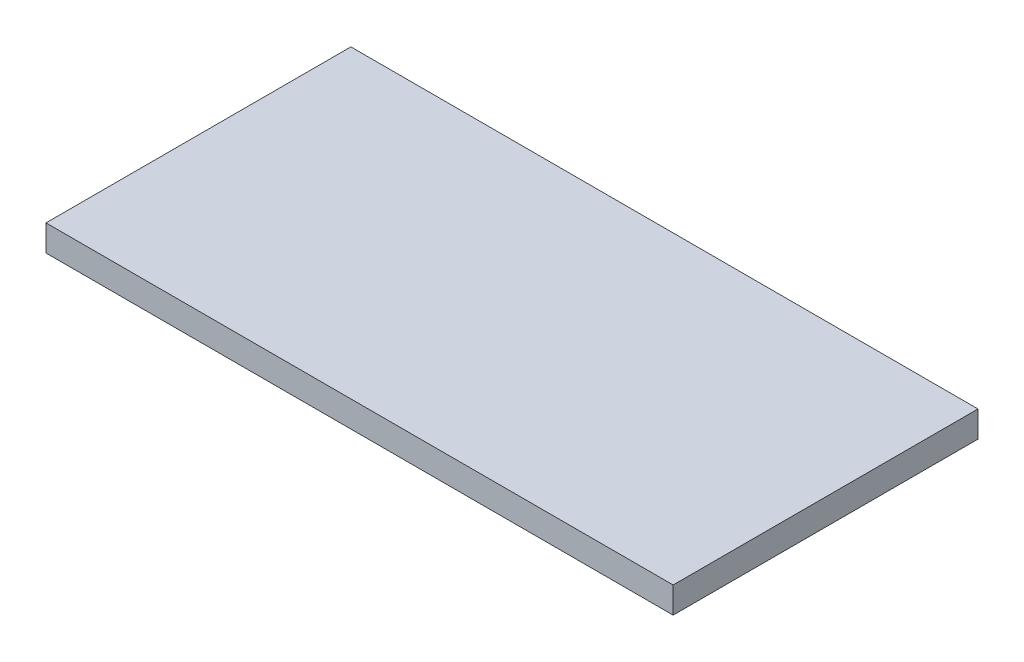
SolidWorks part; units mm, degrees
ref_plane "Спереди" through (0, 0, 0) normal (0, 0, 1) x (1, 0, 0)
ref_plane "Сверху" through (0, 0, 0) normal (0, 1, 0) x (1, 0, 0)
ref_plane "Справа" through (0, 0, 0) normal (1, 0, 0) x (0, 0, -1)
sketch "Эскиз1" plane through (0, 0, 0) normal (0, 1, 0) x (1, 0, 0)
  line L1 (0, 0) -> (720, 0)
  line L2 (0, 0) -> (0, 350)
  line L3 (0, 350) -> (720, 350)
  line L4 (720, 0) -> (720, 350)
extrude "Бобышка-Вытянуть1" add sketch "Эскиз1" along normal blind 30
